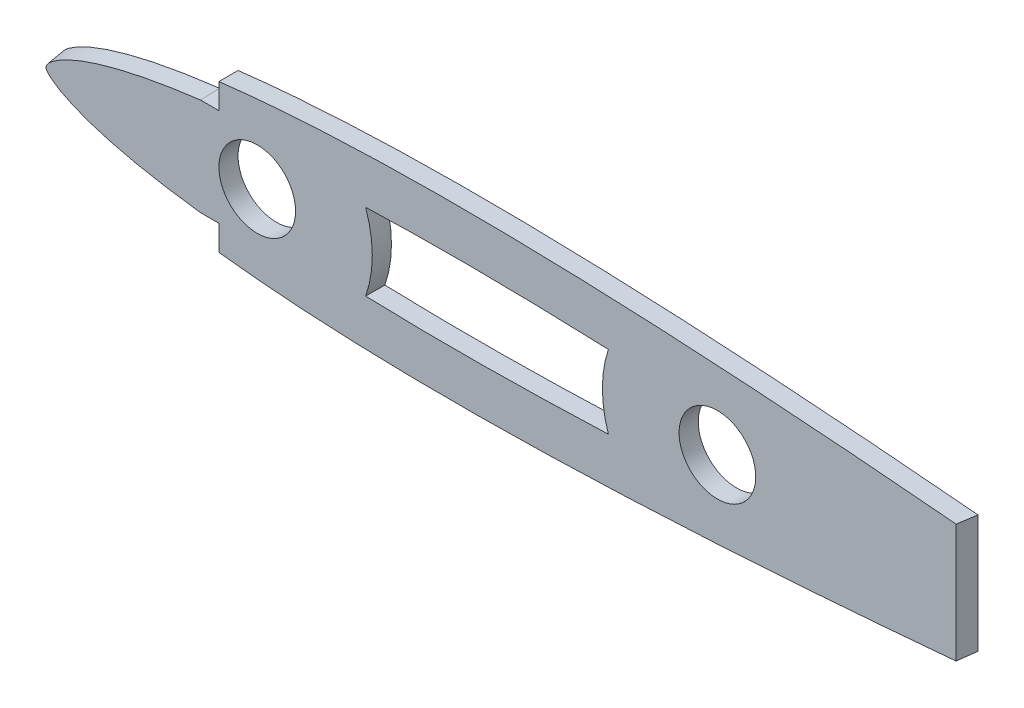
SolidWorks part; units mm, degrees
material "Balsa"
ref_plane "Front Plane" through (0, 0, 0) normal (0, 0, 1) x (1, 0, 0)
ref_plane "Top Plane" through (0, 0, 0) normal (0, 1, 0) x (1, 0, 0)
ref_plane "Right Plane" through (0, 0, 0) normal (1, 0, 0) x (0, 0, -1)
curve "Curve1"
  spline degree 3 poles (237.2261, -0.4007, 0) (237.2261, 0.4007, 0) (236.427, 0.3028, 0) (235.4144, 0.5879, 0) (233.5575, 0.7641, 0) (231.056, 1.1422, 0) (227.8336, 1.5641, 0) (223.9477, 2.0841, 0) (219.4082, 2.6719, 0) (214.2482, 3.3264, 0) (208.4977, 4.0361, 0) (202.1927, 4.7913, 0) (195.3719, 5.5827, 0) (188.0775, 6.3996, 0) (180.3543, 7.2319, 0) (172.25, 8.0693, 0) (163.8146, 8.9011, 0) (155.1002, 9.7155, 0) (146.1603, 10.5018, 0) (137.0502, 11.2469, 0) (127.8259, 11.9387, 0) (118.5443, 12.5643, 0) (109.2626, 13.1106, 0) (100.038, 13.5638, 0) (90.9275, 13.9119, 0) (81.9868, 14.1435, 0) (73.2714, 14.2472, 0) (64.8346, 14.2148, 0) (56.7287, 14.0402, 0) (49.0033, 13.7188, 0) (41.7062, 13.2499, 0) (34.8822, 12.6348, 0) (28.5729, 11.8783, 0) (22.8169, 10.9869, 0) (17.649, 9.97, 0) (13.0996, 8.8388, 0) (9.1945, 7.6047, 0) (5.9535, 6.2789, 0) (3.3869, 4.8705, 0) (1.4988, 3.3767, 0) (0.2895, 1.7614, 0) (-0.1349, 0, 0) (0.2895, -1.7614, 0) (1.4988, -3.3767, 0) (3.3869, -4.8705, 0) (5.9535, -6.2789, 0) (9.1945, -7.6047, 0) (13.0996, -8.8388, 0) (17.649, -9.97, 0) (22.8169, -10.9869, 0) (28.5729, -11.8783, 0) (34.8822, -12.6348, 0) (41.7062, -13.2499, 0) (49.0033, -13.7188, 0) (56.7287, -14.0402, 0) (64.8346, -14.2148, 0) (73.2714, -14.2472, 0) (81.9868, -14.1435, 0) (90.9275, -13.9119, 0) (100.038, -13.5638, 0) (109.2626, -13.1106, 0) (118.5443, -12.5643, 0) (127.8259, -11.9387, 0) (137.0502, -11.2469, 0) (146.1603, -10.5018, 0) (155.1002, -9.7155, 0) (163.8146, -8.9011, 0) (172.25, -8.0693, 0) (180.3543, -7.2319, 0) (188.0775, -6.3996, 0) (195.3719, -5.5827, 0) (202.1927, -4.7913, 0) (208.4977, -4.0361, 0) (214.2482, -3.3264, 0) (219.4082, -2.6719, 0) (223.9477, -2.0841, 0) (227.8336, -1.5641, 0) (231.056, -1.1422, 0) (233.5575, -0.7641, 0) (235.4144, -0.5879, 0) (236.427, -0.3028, 0) (237.2261, -0.4007, 0) (237.2261, 0.4007, 0) (236.427, 0.3028, 0) knots -0.004279 -0.001997 -0.001234 0 0.000762 0.003045 0.006832 0.012101 0.018818 0.026939 0.036415 0.047185 0.05918 0.072328 0.086544 0.101741 0.117823 0.134691 0.15224 0.170361 0.188941 0.207865 0.227016 0.246276 0.265525 0.284645 0.30352 0.322035 0.340078 0.357543 0.374325 0.39033 0.405464 0.419644 0.432793 0.444844 0.455738 0.465429 0.473886 0.481102 0.487102 0.491975 0.495931 0.499383 0.502835 0.50679 0.511664 0.517664 0.524879 0.533337 0.543028 0.553922 0.565972 0.579122 0.593302 0.608436 0.62444 0.641223 0.658687 0.676731 0.695245 0.714121 0.733241 0.75249 0.77175 0.7909 0.809825 0.828404 0.846525 0.864074 0.880942 0.897025 0.912222 0.926438 0.939585 0.951581 0.962351 0.971826 0.979948 0.986664 0.991933 0.995721 0.998003 0.998766 1 1.000762 1.003045 1.006832 periodic
sketch "Sketch1" plane through (0, 0, 0) normal (0, 0, 1) x (1, 0, 0)
  spline S0 degree 3 poles (237.2261, -0.4007) (237.2261, 0.4007) (236.427, 0.3028) (235.4144, 0.5879) (233.5575, 0.7641) (231.056, 1.1422) (227.8336, 1.5641) (223.9477, 2.0841) (219.4082, 2.6719) (214.2482, 3.3264) (208.4977, 4.0361) (202.1927, 4.7913) (195.3719, 5.5827) (188.0775, 6.3996) (180.3543, 7.2319) (172.25, 8.0693) (163.8146, 8.9011) (155.1002, 9.7155) (146.1603, 10.5018) (137.0502, 11.2469) (127.8259, 11.9387) (118.5443, 12.5643) (109.2626, 13.1106) (100.038, 13.5638) (90.9275, 13.9119) (81.9868, 14.1435) (73.2714, 14.2472) (64.8346, 14.2148) (56.7287, 14.0402) (49.0033, 13.7188) (41.7062, 13.2499) (34.8822, 12.6348) (28.5729, 11.8783) (22.8169, 10.9869) (17.649, 9.97) (13.0996, 8.8388) (9.1945, 7.6047) (5.9535, 6.2789) (3.3869, 4.8705) (1.4988, 3.3767) (0.2895, 1.7614) (-0.1349, 0) (0.2895, -1.7614) (1.4988, -3.3767) (3.3869, -4.8705) (5.9535, -6.2789) (9.1945, -7.6047) (13.0996, -8.8388) (17.649, -9.97) (22.8169, -10.9869) (28.5729, -11.8783) (34.8822, -12.6348) (41.7062, -13.2499) (49.0033, -13.7188) (56.7287, -14.0402) (64.8346, -14.2148) (73.2714, -14.2472) (81.9868, -14.1435) (90.9275, -13.9119) (100.038, -13.5638) (109.2626, -13.1106) (118.5443, -12.5643) (127.8259, -11.9387) (137.0502, -11.2469) (146.1603, -10.5018) (155.1002, -9.7155) (163.8146, -8.9011) (172.25, -8.0693) (180.3543, -7.2319) (188.0775, -6.3996) (195.3719, -5.5827) (202.1927, -4.7913) (208.4977, -4.0361) (214.2482, -3.3264) (219.4082, -2.6719) (223.9477, -2.0841) (227.8336, -1.5641) (231.056, -1.1422) (233.5575, -0.7641) (235.4144, -0.5879) (236.427, -0.3028) (237.2261, -0.4007) (237.2261, 0.4007) (236.427, 0.3028) knots -0.004279 -0.001997 -0.001234 0 0.000762 0.003045 0.006832 0.012101 0.018818 0.026939 0.036415 0.047185 0.05918 0.072328 0.086544 0.101741 0.117823 0.134691 0.15224 0.170361 0.188941 0.207865 0.227016 0.246276 0.265525 0.284645 0.30352 0.322035 0.340078 0.357543 0.374325 0.39033 0.405464 0.419644 0.432793 0.444844 0.455738 0.465429 0.473886 0.481102 0.487102 0.491975 0.495931 0.499383 0.502835 0.50679 0.511664 0.517664 0.524879 0.533337 0.543028 0.553922 0.565972 0.579122 0.593302 0.608436 0.62444 0.641223 0.658687 0.676731 0.695245 0.714121 0.733241 0.75249 0.77175 0.7909 0.809825 0.828404 0.846525 0.864074 0.880942 0.897025 0.912222 0.926438 0.939585 0.951581 0.962351 0.971826 0.979948 0.986664 0.991933 0.995721 0.998003 0.998766 1 1.000762 1.003045 1.006832 only from (237.0836, 0.2987) to (237.0836, 0.2987) construction
  spline S1 degree 3 poles (237.2261, -0.4007) (237.2261, 0.4007) (236.427, 0.3028) (235.4144, 0.5879) (233.5575, 0.7641) (231.056, 1.1422) (227.8336, 1.5641) (223.9477, 2.0841) (219.4082, 2.6719) (214.2482, 3.3264) (208.4977, 4.0361) (202.1927, 4.7913) (195.3719, 5.5827) (188.0775, 6.3996) (180.3543, 7.2319) (172.25, 8.0693) (163.8146, 8.9011) (155.1002, 9.7155) (146.1603, 10.5018) (137.0502, 11.2469) (127.8259, 11.9387) (118.5443, 12.5643) (109.2626, 13.1106) (100.038, 13.5638) (90.9275, 13.9119) (81.9868, 14.1435) (73.2714, 14.2472) (64.8346, 14.2148) (56.7287, 14.0402) (49.0033, 13.7188) (41.7062, 13.2499) (34.8822, 12.6348) (28.5729, 11.8783) (22.8169, 10.9869) (17.649, 9.97) (13.0996, 8.8388) (9.1945, 7.6047) (5.9535, 6.2789) (3.3869, 4.8705) (1.4988, 3.3767) (0.2895, 1.7614) (-0.1349, 0) (0.2895, -1.7614) (1.4988, -3.3767) (3.3869, -4.8705) (5.9535, -6.2789) (9.1945, -7.6047) (13.0996, -8.8388) (17.649, -9.97) (22.8169, -10.9869) (28.5729, -11.8783) (34.8822, -12.6348) (41.7062, -13.2499) (49.0033, -13.7188) (56.7287, -14.0402) (64.8346, -14.2148) (73.2714, -14.2472) (81.9868, -14.1435) (90.9275, -13.9119) (100.038, -13.5638) (109.2626, -13.1106) (118.5443, -12.5643) (127.8259, -11.9387) (137.0502, -11.2469) (146.1603, -10.5018) (155.1002, -9.7155) (163.8146, -8.9011) (172.25, -8.0693) (180.3543, -7.2319) (188.0775, -6.3996) (195.3719, -5.5827) (202.1927, -4.7913) (208.4977, -4.0361) (214.2482, -3.3264) (219.4082, -2.6719) (223.9477, -2.0841) (227.8336, -1.5641) (231.056, -1.1422) (233.5575, -0.7641) (235.4144, -0.5879) (236.427, -0.3028) (237.2261, -0.4007) (237.2261, 0.4007) (236.427, 0.3028) knots -0.004279 -0.001997 -0.001234 0 0.000762 0.003045 0.006832 0.012101 0.018818 0.026939 0.036415 0.047185 0.05918 0.072328 0.086544 0.101741 0.117823 0.134691 0.15224 0.170361 0.188941 0.207865 0.227016 0.246276 0.265525 0.284645 0.30352 0.322035 0.340078 0.357543 0.374325 0.39033 0.405464 0.419644 0.432793 0.444844 0.455738 0.465429 0.473886 0.481102 0.487102 0.491975 0.495931 0.499383 0.502835 0.50679 0.511664 0.517664 0.524879 0.533337 0.543028 0.553922 0.565972 0.579122 0.593302 0.608436 0.62444 0.641223 0.658687 0.676731 0.695245 0.714121 0.733241 0.75249 0.77175 0.7909 0.809825 0.828404 0.846525 0.864074 0.880942 0.897025 0.912222 0.926438 0.939585 0.951581 0.962351 0.971826 0.979948 0.986664 0.991933 0.995721 0.998003 0.998766 1 1.000762 1.003045 1.006832 only from (237.0836, 0.2987) to (237.0836, 0.2987)
extrude "Boss-Extrude1" add sketch "Sketch1" along normal blind 3.175
sketch "Sketch2" plane through (0, 0, 3.175) normal (0, 0, 1) x (1, 0, 0)
  circle A0 centre (38.1, 0) radius 6.35
  circle A1 centre (114.3, 0) radius 6.35
  dimension "D1" = 12.7
  dimension "D2" = 12.7
  dimension "D3" = 0
  dimension "D4" = 0
  dimension "D5" = 38.1
  dimension "D6" = 114.3
extrude "Cut-Extrude1" cut sketch "Sketch2" against normal blind 3.175
sketch "Sketch3" plane through (0, 0, 0) normal (0, 1, 0) x (1, 0, 0)
  line L2 (154.2743, 0) -> (153.8276, -3.175)
  line L4 (237.1905, 0) -> (0, 0) construction
  line L5 (237.1905, 0) -> (154.2743, 0)
  line L8 (237.1905, -3.175) -> (237.1905, 0) construction
  line L9 (237.1905, -3.175) -> (237.1905, 0)
  line L11 (153.8276, -3.175) -> (237.1905, -3.175)
extrude "Cut-Extrude2" cut sketch "Sketch3" against normal through all both and the other way through all
sketch "Sketch5" plane through (0, 0, 0) normal (0, 0, -1) x (-1, 0, 0)
  line L0 (-31.75, -11.7736) -> (-31.75, -8.173)
  line L1 (-31.75, -11.7736) -> (-31.75, -8.173)
  line L2 (-28.702, -8.173) -> (-31.75, -8.173)
  line L3 (-28.702, -8.173) -> (-31.75, -8.173)
  line L4 (-31.75, 8.173) -> (-31.75, 11.7736)
  line L5 (-31.75, 8.173) -> (-31.75, 11.7736)
  line L6 (-31.75, 8.173) -> (-28.702, 8.173)
  line L7 (-31.75, 8.173) -> (-28.702, 8.173)
  line L8 (-31.75, 11.7736) -> (-31.75, 14.8587)
  line L9 (-31.75, 14.8587) -> (1.816, 11.7736)
  line L10 (1.816, 11.7736) -> (0.4549, -12.7446)
  line L11 (0.4549, -12.7446) -> (-31.75, -15.9024)
  line L12 (-31.75, -15.9024) -> (-31.75, -11.7736)
  spline S0 degree 3 poles (1922.9425, 444.9353) (-218.2575, -47.1523) (-117.0988, 20.5169) (-24.7906, 7.6566) (-22.844, 7.3585) (-20.908, 7.0325) (-18.9871, 6.677) (-17.0833, 6.2879) (-15.1978, 5.8612) (-13.6488, 5.4708) (-12.4253, 5.1351) (-11.518, 4.8708) (-10.6222, 4.5928) (-9.7397, 4.3001) (-8.8718, 3.9915) (-8.0239, 3.6675) (-7.2012, 3.3286) (-6.4085, 2.974) (-5.6532, 2.6043) (-4.9405, 2.2165) (-4.2792, 1.8093) (-3.6908, 1.4005) (-3.283, 1.0721) (-3.0134, 0.8108) (-2.845, 0.6177) (-2.711, 0.4266) (-2.6274, 0.2633) (-2.5818, 0.118) (-2.5689, 0) (-2.5818, -0.118) (-2.6274, -0.2633) (-2.711, -0.4266) (-2.845, -0.6177) (-3.0134, -0.8108) (-3.2832, -1.0721) (-3.6907, -1.4004) (-4.2792, -1.8093) (-4.9405, -2.2165) (-5.6532, -2.6043) (-6.4085, -2.974) (-7.2012, -3.3286) (-8.0238, -3.6675) (-8.8718, -3.9915) (-9.7397, -4.3001) (-10.6222, -4.5928) (-11.518, -4.8708) (-12.4253, -5.1351) (-13.6488, -5.4708) (-15.1978, -5.8612) (-17.0833, -6.2879) (-18.9871, -6.677) (-20.908, -7.0325) (-22.844, -7.3585) (-24.7905, -7.6566) (-116.1394, -20.3835) (-216.2202, 45.7211) (1930.2923, -410.6134) knots -4.334106 -4.334106 -4.334106 -4.334106 0.03125 0.0625 0.09375 0.125 0.15625 0.1875 0.21875 0.25 0.265625 0.28125 0.296875 0.3125 0.328125 0.34375 0.359375 0.375 0.390625 0.40625 0.421875 0.4375 0.453125 0.460938 0.46875 0.476562 0.484375 0.492188 0.5 0.507812 0.515625 0.523438 0.53125 0.539062 0.546875 0.5625 0.578125 0.59375 0.609375 0.625 0.640625 0.65625 0.671875 0.6875 0.703125 0.71875 0.734375 0.75 0.78125 0.8125 0.84375 0.875 0.90625 0.9375 0.96875 5.287985 5.287985 5.287985 5.287985 only from (-28.702, 8.173) to (-28.702, -8.173)
  spline S1 degree 3 poles (-28.702, 8.173) (-28.0499, 8.0942) (-26.745, 7.9289) (-24.7906, 7.6566) (-22.844, 7.3585) (-20.908, 7.0325) (-18.9871, 6.677) (-17.0833, 6.2879) (-15.1978, 5.8612) (-13.6488, 5.4708) (-12.4253, 5.1351) (-11.518, 4.8708) (-10.6222, 4.5928) (-9.7397, 4.3001) (-8.8718, 3.9915) (-8.0239, 3.6675) (-7.2012, 3.3286) (-6.4085, 2.974) (-5.6532, 2.6043) (-4.9405, 2.2165) (-4.2792, 1.8093) (-3.6908, 1.4005) (-3.283, 1.0721) (-3.0134, 0.8108) (-2.845, 0.6177) (-2.711, 0.4266) (-2.6274, 0.2633) (-2.5818, 0.118) (-2.5689, 0) (-2.5818, -0.118) (-2.6274, -0.2633) (-2.711, -0.4266) (-2.845, -0.6177) (-3.0134, -0.8108) (-3.2832, -1.0721) (-3.6907, -1.4004) (-4.2792, -1.8093) (-4.9405, -2.2165) (-5.6532, -2.6043) (-6.4085, -2.974) (-7.2012, -3.3286) (-8.0238, -3.6675) (-8.8718, -3.9915) (-9.7397, -4.3001) (-10.6222, -4.5928) (-11.518, -4.8708) (-12.4253, -5.1351) (-13.6488, -5.4708) (-15.1978, -5.8612) (-17.0833, -6.2879) (-18.9871, -6.677) (-20.908, -7.0325) (-22.844, -7.3585) (-24.7905, -7.6566) (-26.745, -7.9289) (-28.0499, -8.0942) (-28.702, -8.173) knots 0 0 0 0 0.03125 0.0625 0.09375 0.125 0.15625 0.1875 0.21875 0.25 0.265625 0.28125 0.296875 0.3125 0.328125 0.34375 0.359375 0.375 0.390625 0.40625 0.421875 0.4375 0.453125 0.460938 0.46875 0.476562 0.484375 0.492188 0.5 0.507812 0.515625 0.523438 0.53125 0.539062 0.546875 0.5625 0.578125 0.59375 0.609375 0.625 0.640625 0.65625 0.671875 0.6875 0.703125 0.71875 0.734375 0.75 0.78125 0.8125 0.84375 0.875 0.90625 0.9375 0.96875 1 1 1 1
sketch "Sketch6" plane through (0, 0, 3.175) normal (0, 0, 1) x (1, 0, 0)
  line L0 (31.75, 8.0764) -> (31.75, 11.6833)
  line L1 (31.75, 8.0764) -> (31.75, 11.6833)
  line L2 (28.702, -8.0764) -> (31.75, -8.0764)
  line L3 (28.702, -8.0764) -> (31.75, -8.0764)
  line L4 (31.75, -11.6833) -> (31.75, -8.0764)
  line L5 (31.75, -11.6833) -> (31.75, -8.0764)
  line L6 (31.75, 8.0764) -> (28.702, 8.0764)
  line L7 (31.75, 8.0764) -> (28.702, 8.0764)
  line L8 (31.75, 11.6833) -> (31.75, 18.3959)
  line L9 (31.75, 18.3959) -> (-8.9984, 14.1869)
  line L10 (-8.9984, 14.1869) -> (-8.0322, -19.0612)
  line L11 (-8.0322, -19.0612) -> (31.75, -17.6645)
  line L12 (31.75, -17.6645) -> (31.75, -11.6833)
  spline S0 degree 3 poles (-1926.103, 430.7131) (214.6665, -46.0059) (115.3645, 20.4087) (24.8632, 7.5596) (22.9529, 7.2618) (21.0532, 6.9366) (19.1688, 6.5823) (17.3014, 6.1949) (15.4524, 5.7705) (13.9338, 5.3826) (12.7348, 5.0493) (11.8458, 4.787) (10.9683, 4.5113) (10.1041, 4.2211) (9.2546, 3.9154) (8.4251, 3.5946) (7.6208, 3.2593) (6.8465, 2.9089) (6.1095, 2.544) (5.4151, 2.1619) (4.7717, 1.7612) (4.2006, 1.3602) (3.8064, 1.0398) (3.5462, 0.7856) (3.3839, 0.5981) (3.2548, 0.4126) (3.1742, 0.2543) (3.1304, 0.1138) (3.118, 0) (3.1304, -0.1138) (3.1742, -0.2543) (3.2548, -0.4126) (3.3839, -0.5981) (3.5462, -0.7856) (3.8065, -1.0398) (4.2006, -1.3601) (4.7718, -1.7612) (5.4151, -2.1619) (6.1095, -2.5441) (6.8464, -2.9089) (7.6208, -3.2593) (8.425, -3.5945) (9.2546, -3.9154) (10.1041, -4.2211) (10.9683, -4.5113) (11.8458, -4.787) (12.7348, -5.0493) (13.9339, -5.3826) (15.4524, -5.7705) (17.3014, -6.1949) (19.1688, -6.5823) (21.0532, -6.9366) (22.9529, -7.2618) (24.8631, -7.5596) (114.4091, -20.2734) (212.6358, 44.5789) (-1933.1174, -396.4449) knots -4.329585 -4.329585 -4.329585 -4.329585 0.03125 0.0625 0.09375 0.125 0.15625 0.1875 0.21875 0.25 0.265625 0.28125 0.296875 0.3125 0.328125 0.34375 0.359375 0.375 0.390625 0.40625 0.421875 0.4375 0.453125 0.460938 0.46875 0.476562 0.484375 0.492188 0.5 0.507812 0.515625 0.523438 0.53125 0.539062 0.546875 0.5625 0.578125 0.59375 0.609375 0.625 0.640625 0.65625 0.671875 0.6875 0.703125 0.71875 0.734375 0.75 0.78125 0.8125 0.84375 0.875 0.90625 0.9375 0.96875 5.282783 5.282783 5.282783 5.282783 only from (28.702, 8.0764) to (28.702, -8.0764)
  spline S1 degree 3 poles (28.702, 8.0764) (28.062, 7.9974) (26.7814, 7.8319) (24.8632, 7.5596) (22.9529, 7.2618) (21.0532, 6.9366) (19.1688, 6.5823) (17.3014, 6.1949) (15.4524, 5.7705) (13.9338, 5.3826) (12.7348, 5.0493) (11.8458, 4.787) (10.9683, 4.5113) (10.1041, 4.2211) (9.2546, 3.9154) (8.4251, 3.5946) (7.6208, 3.2593) (6.8465, 2.9089) (6.1095, 2.544) (5.4151, 2.1619) (4.7717, 1.7612) (4.2006, 1.3602) (3.8064, 1.0398) (3.5462, 0.7856) (3.3839, 0.5981) (3.2548, 0.4126) (3.1742, 0.2543) (3.1304, 0.1138) (3.118, 0) (3.1304, -0.1138) (3.1742, -0.2543) (3.2548, -0.4126) (3.3839, -0.5981) (3.5462, -0.7856) (3.8065, -1.0398) (4.2006, -1.3601) (4.7718, -1.7612) (5.4151, -2.1619) (6.1095, -2.5441) (6.8464, -2.9089) (7.6208, -3.2593) (8.425, -3.5945) (9.2546, -3.9154) (10.1041, -4.2211) (10.9683, -4.5113) (11.8458, -4.787) (12.7348, -5.0493) (13.9339, -5.3826) (15.4524, -5.7705) (17.3014, -6.1949) (19.1688, -6.5823) (21.0532, -6.9366) (22.9529, -7.2618) (24.8631, -7.5596) (26.7813, -7.8319) (28.062, -7.9974) (28.702, -8.0764) knots 0 0 0 0 0.03125 0.0625 0.09375 0.125 0.15625 0.1875 0.21875 0.25 0.265625 0.28125 0.296875 0.3125 0.328125 0.34375 0.359375 0.375 0.390625 0.40625 0.421875 0.4375 0.453125 0.460938 0.46875 0.476562 0.484375 0.492188 0.5 0.507812 0.515625 0.523438 0.53125 0.539062 0.546875 0.5625 0.578125 0.59375 0.609375 0.625 0.640625 0.65625 0.671875 0.6875 0.703125 0.71875 0.734375 0.75 0.78125 0.8125 0.84375 0.875 0.90625 0.9375 0.96875 1 1 1 1
loft "Cut-Loft1" cut profiles "Sketch6", "Sketch5"
sketch "Sketch7" plane through (0, 0, 3.175) normal (0, 0, 1) x (1, 0, 0)
  line L2 (146.2076, -2.8409) -> (146.2076, 2.8409)
  arc A3 (56.0542, -6.3678) -> (56.0542, 6.3678) centre (38.1, 0) ccw
  arc A4 (96.2458, 6.0785) -> (96.2458, -6.0785) centre (114.3, 0) ccw
  spline S7 degree 3 poles (96.2458, 6.0785) (93.8614, 6.1723) (91.4778, 6.2553) (84.3446, 6.4683) (79.5987, 6.5623) (70.1215, 6.6291) (65.3899, 6.6022) (59.1317, 6.4625) (57.592, 6.4198) (56.0542, 6.3678) knots 0.43731 0.43731 0.43731 0.43731 0.5 0.5 0.625 0.625 0.75 0.75 0.790836 0.790836 0.790836 0.790836
  spline S8 degree 3 poles (1861.9599, 2350.2628) (-219.6941, 152.781) (-109.3199, 7.6586) (41.9044, -5.6026) (44.2362, -5.7741) (51.2512, -6.2083) (55.9556, -6.3916) (65.3899, -6.6022) (70.1215, -6.6291) (79.5987, -6.5623) (84.3446, -6.4683) (98.5966, -6.0428) (108.1137, -5.5705) (568.8842, 23.3346) (1029.7944, 331.9743) (829.5056, -2718.7599) knots -3.947268 -3.947268 -3.947268 -3.947268 0.0625 0.0625 0.125 0.125 0.25 0.25 0.375 0.375 0.5 0.5 0.75 0.75 12.597732 12.597732 12.597732 12.597732 only from (32.6569, -4.6849) to (146.2076, -2.8409)
  spline S9 degree 3 poles (829.5102, 2718.6907) (1029.7875, -331.9696) (568.8808, -23.3344) (108.1137, 5.5705) (98.5966, 6.0428) (84.3446, 6.4683) (79.5987, 6.5623) (70.1215, 6.6291) (65.3899, 6.6022) (55.9556, 6.3916) (51.2512, 6.2083) (44.2362, 5.7741) (41.9044, 5.6026) (-109.3184, -7.6584) (-219.6918, -152.7781) (1861.8973, -2350.1967) knots -11.597643 -11.597643 -11.597643 -11.597643 0.25 0.25 0.5 0.5 0.625 0.625 0.75 0.75 0.875 0.875 0.9375 0.9375 4.947227 4.947227 4.947227 4.947227 only from (146.2076, 2.8409) to (32.6569, 4.6849)
  spline S10 degree 3 poles (56.0542, -6.3678) (57.592, -6.4198) (59.1317, -6.4625) (65.3899, -6.6022) (70.1215, -6.6291) (79.5987, -6.5623) (84.3446, -6.4683) (91.4778, -6.2553) (93.8614, -6.1723) (96.2458, -6.0785) knots 0.209164 0.209164 0.209164 0.209164 0.25 0.25 0.375 0.375 0.5 0.5 0.56269 0.56269 0.56269 0.56269
  dimension "D1" = 7.62
extrude "Cut-Extrude3" cut sketch "Sketch7" against normal blind 7.62
